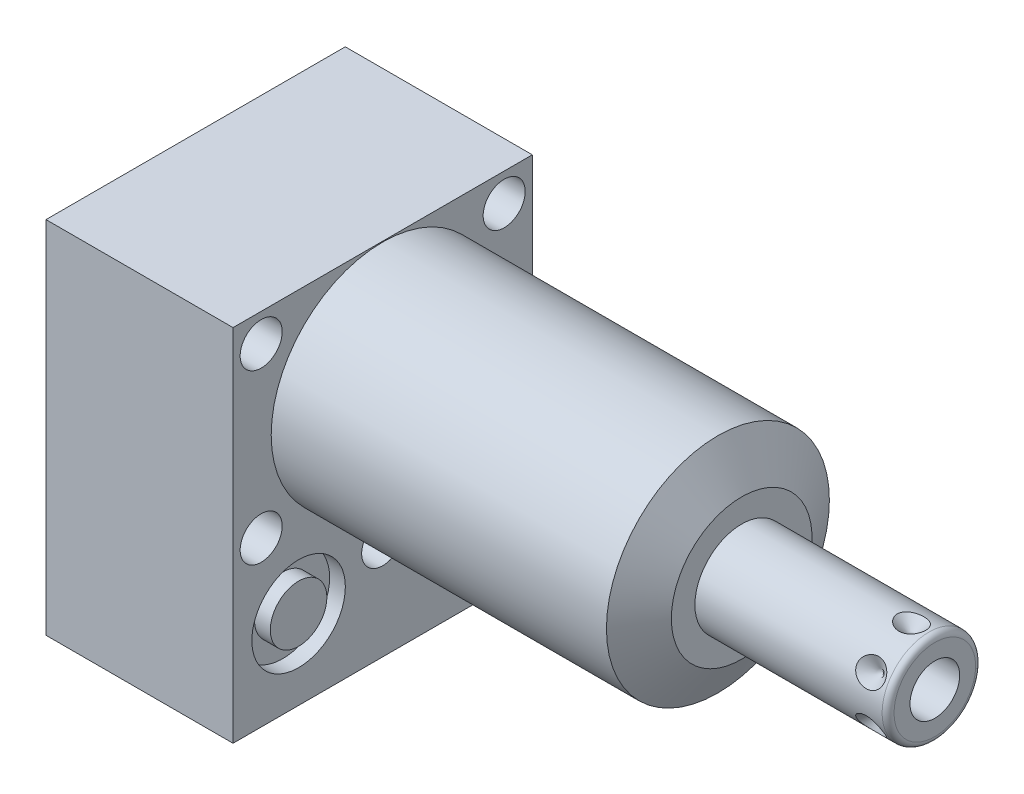
SolidWorks part; units mm, degrees
material "Alloy Steel"
ref_plane "Front Plane" through (0, 0, 0) normal (0, 0, 1) x (1, 0, 0)
ref_plane "Top Plane" through (0, 0, 0) normal (0, 1, 0) x (1, 0, 0)
ref_plane "Right Plane" through (0, 0, 0) normal (1, 0, 0) x (0, 0, -1)
ref_plane "Plane1" through (0, 0, 0) normal (1, 0, 0) x (0, 0, -1)
sketch "Sketch1" plane through (0, 0, 0) normal (1, 0, 0) x (0, 0, -1)
  line L0 (-25.4, 19.05) -> (-25.4, -42.0624)
  line L1 (-25.4, -42.0624) -> (25.4, -42.0624)
  line L2 (25.4, -42.0624) -> (25.4, 19.05)
  line L3 (25.4, 19.05) -> (-25.4, 19.05)
  line L4 (0, -47.0916) -> (0, 22.1996) construction
  dimension "D1" = 50.8
  dimension "D2" = 61.1124
  dimension "D3" = 19.05
extrude "Extrude1" add sketch "Sketch1" along normal blind 60.9346 and the other way blind 31.75
ref_plane "Plane2" through (0, 0, 0) normal (1, 0, 0) x (0, 0, -1)
sketch "Sketch2" plane through (0, 0, 0) normal (1, 0, 0) x (0, 0, -1)
  line L0 (-20.8153, 0) -> (20.8153, 0) construction
  line L6 (25.4, 19.05) -> (-25.4, 19.05)
  line L7 (-25.4, 19.05) -> (-25.4, -42.0624)
  line L8 (-25.4, -42.0624) -> (25.4, -42.0624)
  line L9 (25.4, -42.0624) -> (25.4, 19.05)
  line L10 (25.4, 19.05) -> (-25.4, 19.05)
  line L11 (-25.4, 19.05) -> (-25.4, -42.0624)
  line L12 (-25.4, -42.0624) -> (25.4, -42.0624)
  line L13 (25.4, -42.0624) -> (25.4, 19.05)
  circle A0 centre (0, 0) radius 18.923
  dimension "D1" = 37.846
  dimension "D2" = 0
extrude "Cut-Extrude1" cut sketch "Sketch2" along normal up to next
ref_plane "Plane3" through (0, 0, 0) normal (0, 0, 1) x (1, 0, 0)
sketch "Sketch3" plane through (0, 0, 0) normal (0, 0, 1) x (1, 0, 0)
  line L0 (56.9018, 18.923) -> (60.9346, 11.938)
  line L1 (56.7002, 0) -> (61.1362, 0) construction
  line L2 (60.9346, 18.923) -> (60.9346, 11.938)
  line L3 (60.9346, 18.923) -> (56.9018, 18.923)
  line L4 (60.9346, 18.923) -> (0, 18.923) construction
  line L5 (60.9346, -18.923) -> (60.9346, 18.923) construction
  dimension "D1" = 23.876
  dimension "D2" = 30
revolve "Cut-Revolve1" cut sketch "Sketch3" angle 360 about L1
ref_plane "Plane4" through (-29.083, -28.575, 14.2748) normal (0, 0, 1) x (0, 1, 0)
sketch "S2D0002" plane through (-29.083, -28.575, 14.2748) normal (0, 0, 1) x (0, 1, 0)
  line L0 (0, 0) -> (4.5466, 0)
  line L1 (4.5466, 0) -> (4.1066, -2.0701)
  line L2 (4.1066, -2.0701) -> (3.4544, -2.7223)
  line L3 (3.4544, -2.7223) -> (3.4544, -13.97)
  line L4 (3.4544, -13.97) -> (0, -13.97)
  line L5 (0, -13.97) -> (0, 0)
  line L6 (0, -14.6685) -> (0, 0.6985) construction
  dimension "D1" = 13.97
revolve "Cut-Revolve2" cut sketch "S2D0002" angle 360 about L6
ref_plane "Plane5" through (-29.083, -28.575, -14.2748) normal (0, 0, 1) x (0, 1, 0)
sketch "Sketch5" plane through (-29.083, -28.575, -14.2748) normal (0, 0, 1) x (0, 1, 0)
  line L0 (0, 0) -> (4.5466, 0)
  line L1 (4.5466, 0) -> (4.1066, -2.0701)
  line L2 (4.1066, -2.0701) -> (3.4544, -2.7223)
  line L3 (3.4544, -2.7223) -> (3.4544, -13.97)
  line L4 (3.4544, -13.97) -> (0, -13.97)
  line L5 (0, -13.97) -> (0, 0)
  line L6 (0, -14.6685) -> (0, 0.6985) construction
  dimension "D1" = 13.97
revolve "Cut-Revolve3" cut sketch "Sketch5" angle 360 about L6
ref_plane "Plane6" through (-2.667, -28.575, 14.2748) normal (0, 0, 1) x (0, -1, 0)
sketch "Sketch6" plane through (-2.667, -28.575, 14.2748) normal (0, 0, 1) x (0, -1, 0)
  line L0 (0, 0) -> (4.5466, 0)
  line L1 (4.5466, 0) -> (4.1066, -2.0701)
  line L2 (4.1066, -2.0701) -> (3.4544, -2.7223)
  line L3 (3.4544, -2.7223) -> (3.4544, -12.192)
  line L4 (3.4544, -12.192) -> (0, -12.192)
  line L5 (0, -12.192) -> (0, 0)
  line L6 (0, -12.8016) -> (0, 0.6096) construction
  dimension "D1" = 12.192
revolve "Cut-Revolve4" cut sketch "Sketch6" angle 360 about L6
ref_plane "Plane7" through (-2.667, -28.575, -14.2748) normal (0, 0, 1) x (0, -1, 0)
sketch "Sketch7" plane through (-2.667, -28.575, -14.2748) normal (0, 0, 1) x (0, -1, 0)
  line L0 (0, 0) -> (4.5466, 0)
  line L1 (4.5466, 0) -> (4.1066, -2.0701)
  line L2 (4.1066, -2.0701) -> (3.4544, -2.7223)
  line L3 (3.4544, -2.7223) -> (3.4544, -12.192)
  line L4 (3.4544, -12.192) -> (0, -12.192)
  line L5 (0, -12.192) -> (0, 0)
  line L6 (0, -12.8016) -> (0, 0.6096) construction
  dimension "D1" = 12.192
revolve "Cut-Revolve5" cut sketch "Sketch7" angle 360 about L6
ref_plane "Plane8" through (-15.875, -43.688, 14.2748) normal (0, 0, 1) x (-1, 0, 0)
sketch "Sketch18" plane through (-31.75, 0, 0) normal (-1, 0, 0) x (0, 0, 1)
  circle A0 centre (-14.2748, -28.575) radius 7.9375
  circle A1 centre (14.2748, -28.575) radius 7.9375
  dimension "D1" = 15.875
  dimension "D2" = 15.875
extrude "Cut-Extrude2" cut sketch "Sketch18" against normal blind 2.667
sketch "Sketch19" plane through (0, 0, 0) normal (1, 0, 0) x (0, 0, -1)
  circle A0 centre (-14.2748, -28.575) radius 7.9375
  circle A1 centre (14.2748, -28.575) radius 7.9375
  dimension "D1" = 15.875
  dimension "D2" = 15.875
extrude "Cut-Extrude3" cut sketch "Sketch19" against normal blind 2.667
sketch "Sketch8" plane through (-15.875, -43.688, 14.2748) normal (0, 0, 1) x (-1, 0, 0)
  line L0 (0, -1.8796) -> (6.1849, -1.8796)
  line L1 (6.1849, -1.8796) -> (5.6423, -4.4323)
  line L2 (5.6423, -4.4323) -> (4.9784, -5.0962)
  line L3 (4.9784, -5.0962) -> (4.9784, -20.9296)
  line L4 (4.9784, -20.9296) -> (0, -20.9296)
  line L5 (0, -20.9296) -> (0, -1.8796)
  line L6 (0, -26.67) -> (0, 1.27) construction
  line L7 (15.875, -1.6256) -> (-15.875, -1.6256) construction
  dimension "D1" = 19.05
  dimension "D2" = 0.254
revolve "Cut-Revolve6" cut sketch "Sketch8" angle 360 about L6
ref_plane "Plane9" through (-15.875, -43.688, -14.2748) normal (0, 0, 1) x (-1, 0, 0)
sketch "Sketch9" plane through (-15.875, -43.688, -14.2748) normal (0, 0, 1) x (-1, 0, 0)
  line L0 (0, -1.8796) -> (6.1849, -1.8796)
  line L1 (6.1849, -1.8796) -> (5.6423, -4.4323)
  line L2 (5.6423, -4.4323) -> (4.9784, -5.0962)
  line L3 (4.9784, -5.0962) -> (4.9784, -20.9296)
  line L4 (4.9784, -20.9296) -> (0, -20.9296)
  line L5 (0, -20.9296) -> (0, -1.8796)
  line L6 (0, -26.67) -> (0, 1.27) construction
  line L7 (15.875, -1.6256) -> (-15.875, -1.6256) construction
  dimension "D1" = 19.05
  dimension "D2" = 0.254
revolve "Cut-Revolve7" cut sketch "Sketch9" angle 360 about L6
ref_plane "Plane10" through (0, 0, 0) normal (0, 0, 1) x (1, 0, 0)
sketch "Sketch20" plane through (0, -42.0624, 0) normal (0, -1, 0) x (1, 0, 0)
  circle A0 centre (-15.875, 14.2748) radius 9.525
  circle A1 centre (-15.875, -14.2748) radius 9.525
  dimension "D1" = 19.05
extrude "Cut-Extrude4" cut sketch "Sketch20" against normal blind 0.254
sketch "Sketch10" plane through (0, 0, 0) normal (0, 0, 1) x (1, 0, 0)
  line L0 (60.9346, 0) -> (60.9346, 7.9375)
  line L1 (60.9346, 7.9375) -> (92.71, 7.9375)
  line L2 (93.726, 6.9215) -> (93.726, 0)
  line L3 (93.726, 0) -> (60.9346, 0)
  line L4 (59.5935, 0) -> (89.0981, 0) construction
  line L5 (60.9346, -11.938) -> (60.9346, 11.938) construction
  line L6 (-31.75, 19.05) -> (-31.75, -42.0624) construction
  arc A0 (93.726, 6.9215) -> (92.71, 7.9375) centre (92.71, 6.9215) ccw
  point P0 (60.9346, 0)
  dimension "D2" = 1.016
  dimension "D1" = 15.875
  dimension "D3" = 125.476
revolve "Revolve1" add sketch "Sketch10" angle 360 about L4
ref_plane "Plane11" through (87.757, -4.2164, 0) normal (0, 0, 1) x (0, -1, 0)
sketch "S2D0001" plane through (87.757, -4.2164, 0) normal (0, 0, 1) x (0, -1, 0)
  line L0 (0, 5.969) -> (0, -9.271)
  line L1 (0, -9.271) -> (-4.2164, -11.8045)
  line L2 (0, 5.969) -> (-4.2164, 5.969)
  line L3 (-4.2164, 5.969) -> (-4.2164, -11.8045)
  line L4 (-4.2164, -24.865) -> (-4.2164, 0.8887) construction
  line L5 (2.7051, 5.969) -> (-11.1379, 5.969) construction
  dimension "D1" = 8.4328
  dimension "D2" = 59
  dimension "D3" = 15.24
revolve "Cut-Revolve8" cut sketch "S2D0001" angle 360 about L4
ref_plane "Plane12" through (-31.75, -43.688, 0) normal (0, -1, 0) x (0, 0, -1)
sketch "Sketch12" plane through (-31.75, -41.8084, 0) normal (0, -1, 0) x (0, 0, -1)
  circle A0 centre (-14.2748, 15.875) radius 6.4389
  circle A1 centre (-14.2748, 15.875) radius 9.525 construction
  dimension "D1" = 12.8778
extrude "Extrude2" add sketch "Sketch12" along normal blind 1.651
sketch "Sketch13" plane through (0, 0, 0) normal (1, 0, 0) x (0, 0, -1)
  circle A0 centre (-14.2748, -28.575) radius 4.8006
  circle A1 centre (-14.2748, -28.575) radius 4.5466 construction
  dimension "D1" = 9.6012
ref_plane "Plane13" through (-31.75, 0, 0) normal (1, 0, 0) x (0, 0, -1)
extrude "Extrude3" add sketch "Sketch13" along normal up to surface (2.667 mm away)
ref_plane "Plane14" through (0, -28.575, -14.2748) normal (0, -1, 0) x (0, 0, -1)
sketch "Sketch14" plane through (0, -28.575, -14.2748) normal (0, -1, 0) x (0, 0, -1)
  line L0 (0, -2.8435) -> (0, 1.0401) construction
  line L1 (0, -2.667) -> (0, -4.7371) construction
  line L2 (7.9375, -2.667) -> (-7.9375, -2.667) construction
  circle A0 centre (6.1722, -0.9017) radius 1.7653
  dimension "D1" = 3.5306
  dimension "D2" = 12.3444
revolve "Revolve2" add sketch "Sketch14" angle 360 about L0
ref_plane "Plane15" through (0, -28.575, -14.2748) normal (0, -1, 0) x (0, 0, -1)
sketch "Sketch15" plane through (0, -28.575, -14.2748) normal (0, -1, 0) x (0, 0, -1)
  line L0 (0, -32.7901) -> (0, -28.9065) construction
  line L1 (0, -26.3607) -> (0, -19.4599) construction
  line L2 (-7.9375, -29.083) -> (7.9375, -29.083) construction
  circle A0 centre (6.1722, -30.8483) radius 1.7653
  dimension "D1" = 3.5306
  dimension "D2" = 12.3444
revolve "Revolve3" add sketch "Sketch15" angle 360 about L0
ref_plane "Plane16" through (83.7946, -7.9375, 0) normal (0, 0, 1) x (-1, 0, 0)
sketch "Sketch16" plane through (83.7946, -7.9375, 0) normal (0, 0, 1) x (-1, 0, 0)
  line L0 (-5.969, 0) -> (-3.556, 0)
  line L1 (-3.556, 0) -> (-5.969, -2.413)
  line L2 (-5.969, 0) -> (-5.969, -2.413)
  line L3 (-5.969, -3.8054) -> (-5.969, 0.1207) construction
  line L4 (22.86, 0) -> (-8.9154, 0) construction
  line L5 (-9.9314, -1.016) -> (-9.9314, -14.859) construction
  dimension "D1" = 3.9624
  dimension "D2" = 4.826
  dimension "D3" = 45
revolve "Cut-Revolve9" cut sketch "Sketch16" angle 360 about L3
pattern_circular "CirPattern1" count 6 over 360 about axis through (60.9356, 0, 0) along (-1, 0, 0) of "Cut-Revolve9"
hole_wizard "Hole1" positions "Sketch22" profile "Sketch21" legacy end condition up to next
sketch "Sketch22" plane through (0, 0, 0) normal (1, 0, 0) x (0, 0, -1)
  line L0 (0, 0) -> (-32.1908, 0) construction
  point P0 (-20.6248, 14.2748)
  point P1 (0, -25.0952)
  point P13 (-20.6248, -14.2748)
  point P14 (20.6248, 14.2748)
  point P15 (20.6248, -14.2748)
  dimension "D2" = 14.2748
  dimension "D3" = 25.0952
sketch "Sketch21" plane through (0, 14.2748, 20.6248) normal (0, 1, 0) x (0, 0, -1)
  line L0 (0, 0) -> (0, 31.75)
  line L1 (0, 31.75) -> (3.5687, 31.75)
  line L2 (3.5687, 31.75) -> (3.5687, 0)
  line L3 (3.5687, 0) -> (0, 0)
  line L4 (0, 110) -> (0, -10) construction
  dimension "Diameter" = 7.1374
  dimension "Depth" = 31.75
sketch "Sketch24" plane through (-29.083, 0, 0) normal (-1, 0, 0) x (0, 0, 1)
  circle A0 centre (14.2748, -28.575) radius 4.8006
  dimension "D1" = 9.6012
extrude "Extrude4" add sketch "Sketch24" along normal blind 2.667
